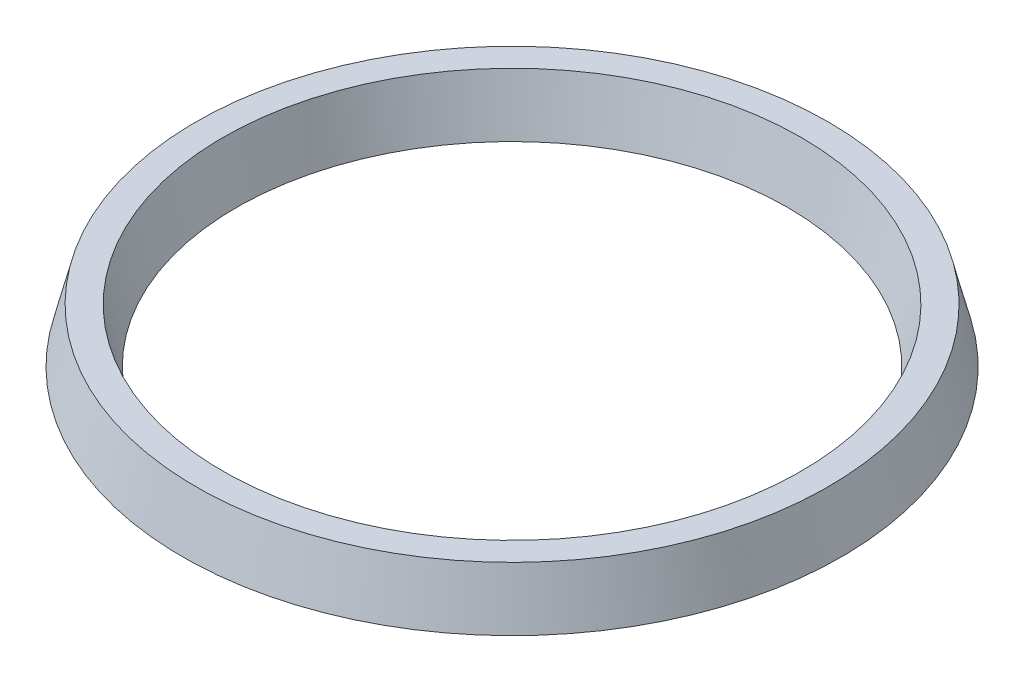
SolidWorks part; units mm, degrees
ref_plane "Front Plane" through (0, 0, 0) normal (0, 0, 1) x (1, 0, 0)
ref_plane "Top Plane" through (0, 0, 0) normal (0, 1, 0) x (1, 0, 0)
ref_plane "Right Plane" through (0, 0, 0) normal (1, 0, 0) x (0, 0, -1)
sketch "Sketch1" plane through (0, 0, 0) normal (1, 0, 0) x (0, 0, -1)
  line L0 (-3.365, 0) -> (-11524.9254, 0) construction
  line L1 (0, 0) -> (0, 11521.5604) construction
  line L2 (64.31, 6) -> (70.31, 6)
  line L3 (67.31, 0) -> (67.31, 11521.5604) construction
  line L4 (70.31, 6) -> (73.31, -6)
  line L5 (73.31, -6) -> (70.31, -6)
  line L6 (61.31, -6) -> (64.31, -6)
  line L7 (64.31, 6) -> (61.31, -6)
  line L8 (64.31, -6) -> (65.4462, -1.4552)
  line L9 (69.1738, -1.4552) -> (70.31, -6)
  arc A0 (65.4462, -1.4552) -> (69.1738, -1.4552) centre (67.31, -1.9212) cw
  point P10 (67.31, 6)
  point P17 (0, 0)
  dimension "D1" = 6
  dimension "D2" = 140.62
  dimension "D3" = 146.62
  dimension "D4" = 3
  dimension "D5" = 12
  dimension "D6" = 6
revolve "Revolve1" add sketch "Sketch1" angle 360 about L1
